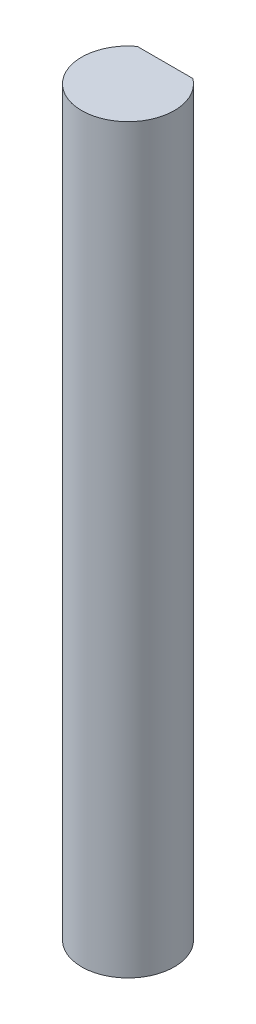
SolidWorks part; units mm, degrees
ref_plane "Front Plane" through (0, 0, 0) normal (0, 0, 1) x (1, 0, 0)
ref_plane "Top Plane" through (0, 0, 0) normal (0, 1, 0) x (1, 0, 0)
ref_plane "Right Plane" through (0, 0, 0) normal (1, 0, 0) x (0, 0, -1)
sketch "Sketch1" plane through (0, 0, 0) normal (0, 1, 0) x (1, 0, 0)
  line L0 (-1.905, 2.54) -> (1.905, 2.54)
  arc A0 (-1.905, 2.54) -> (1.905, 2.54) centre (0, 0) ccw
  dimension "D1" = 6.35
  dimension "D2" = 2.54
extrude "Boss-Extrude1" add sketch "Sketch1" along normal blind 50.8
